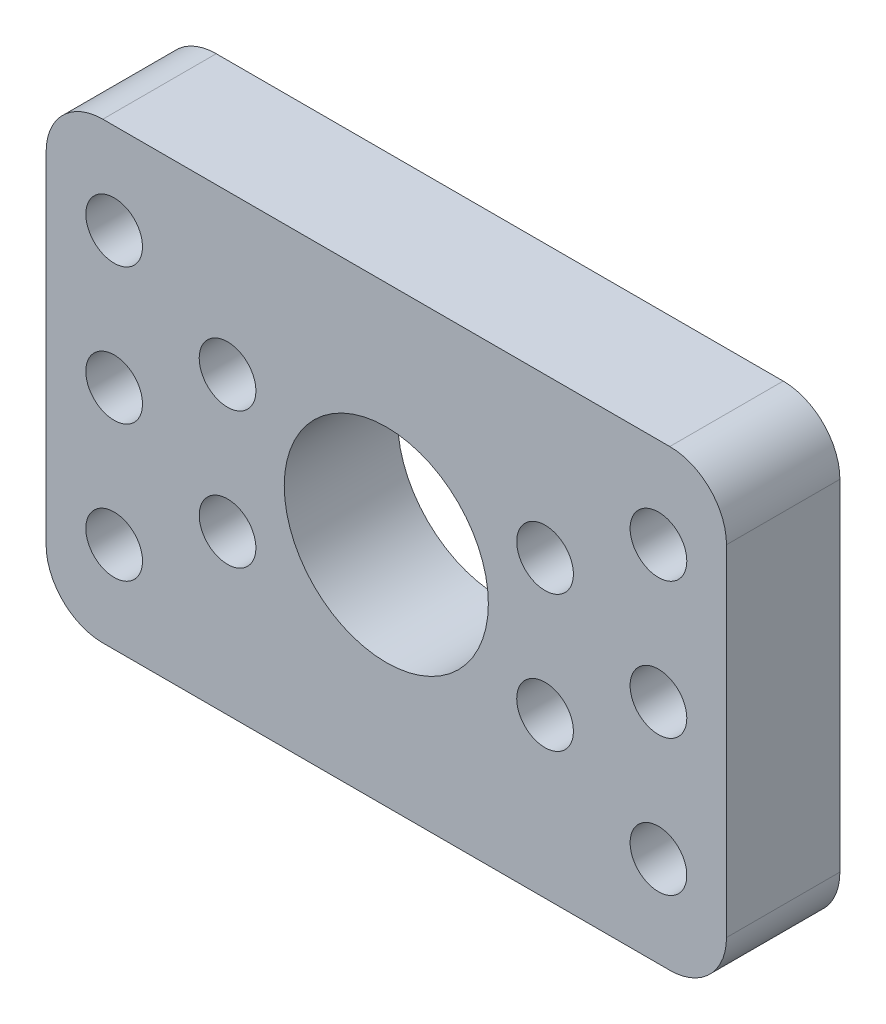
SolidWorks part; units mm, degrees
ref_plane "正面(Front)" through (0, 0, 0) normal (0, 0, 1) x (1, 0, 0)
ref_plane "平面(Top)" through (0, 0, 0) normal (0, 1, 0) x (1, 0, 0)
ref_plane "右側面(Right)" through (0, 0, 0) normal (1, 0, 0) x (0, 0, -1)
sketch "ｽｹｯﾁ1" plane through (0, 0, 0) normal (0, 0, 1) x (1, 0, 0)
  line L1 (-25, 20) -> (25, 20)
  line L2 (-30, 15) -> (-30, -15)
  line L3 (-25, -20) -> (25, -20)
  line L4 (30, 15) -> (30, -15)
  line L5 (-30, 20) -> (30, -20) construction
  line L6 (-30, -20) -> (30, 20) construction
  circle A0 centre (0, 0) radius 9
  arc A1 (25, 20) -> (30, 15) centre (25, 15) cw
  arc A2 (25, -20) -> (30, -15) centre (25, -15) ccw
  arc A3 (-30, -15) -> (-25, -20) centre (-25, -15) ccw
  arc A4 (-25, 20) -> (-30, 15) centre (-25, 15) ccw
  dimension "D1" = 18
  dimension "D4" = 5
  dimension "D2" = 60
  dimension "D3" = 40
extrude "ﾎﾞｽ - 押し出し1" add sketch "ｽｹｯﾁ1" along normal blind 10
sketch "ｽｹｯﾁ3" plane through (0, 0, 10) normal (0, 0, 1) x (1, 0, 0)
  line L0 (0, 0) -> (37.8188, 0) construction
  circle A0 centre (14, 6) radius 2.5
  circle A1 centre (24, 0) radius 2.5
  circle A2 centre (24, 12) radius 2.5
  circle A4 centre (0, 0) radius 9 construction
  circle A5 centre (24, -12) radius 2.5
  circle A6 centre (14, -6) radius 2.5
  point P9 (25.2644, 0)
  point P10 (21.6238, 0)
  point P11 (21.6238, 12)
  point P14 (0, 0)
  dimension "D1" = 5
  dimension "D2" = 6
  dimension "D3" = 12
  dimension "D4" = 5
  dimension "D5" = 10
extrude "ｶｯﾄ - 押し出し1" cut sketch "ｽｹｯﾁ3" against normal through all
mirror "ﾐﾗｰ1" about plane through (0, 0, 0) normal (1, 0, 0) of "ｶｯﾄ - 押し出し1"
